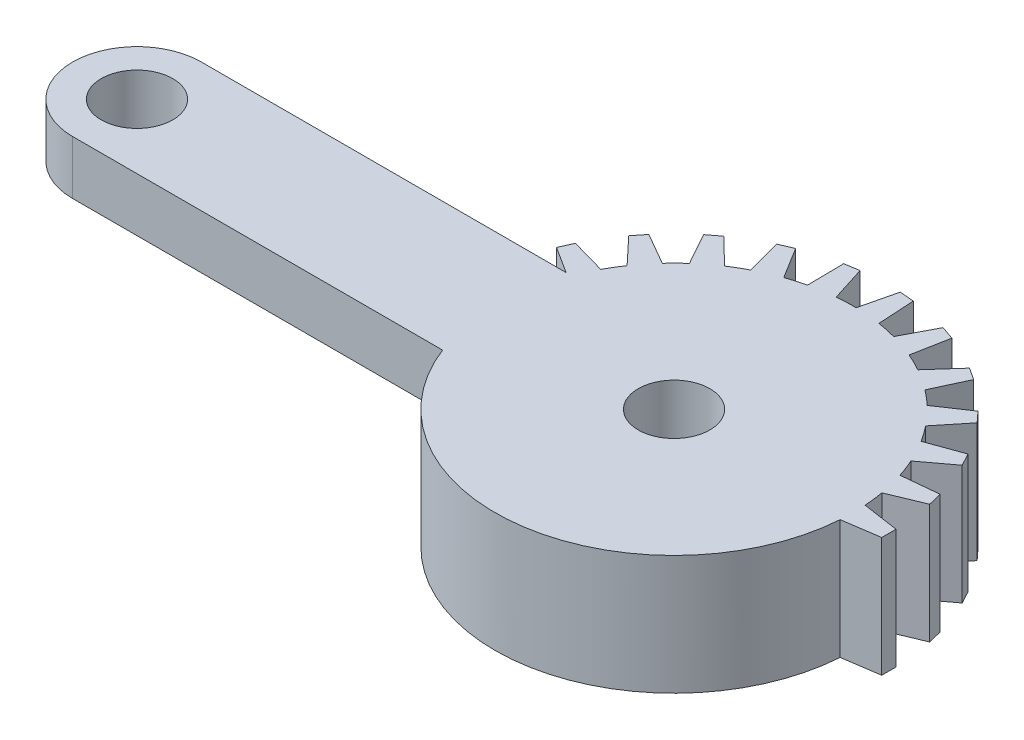
SolidWorks part; units mm, degrees
ref_plane "Front" through (0, 0, 0) normal (0, 0, 1) x (1, 0, 0)
ref_plane "Top" through (0, 0, 0) normal (0, 1, 0) x (1, 0, 0)
ref_plane "Right" through (0, 0, 0) normal (1, 0, 0) x (0, 0, -1)
sketch "Sketch1" plane through (0, 0, 0) normal (0, 1, 0) x (1, 0, 0)
  line L0 (-177.6425, 0) -> (70.7426, 0) construction
  line L1 (-150, 18) -> (-46.6476, 18)
  line L2 (-150, -18) -> (-46.6476, -18)
  arc A0 (-46.6476, -18) -> (-46.6476, 18) centre (0, 0) ccw
  arc A1 (-150, 18) -> (-150, -18) centre (-150, 0) ccw
  dimension "D1" = 100
  dimension "D3" = 150
  dimension "D2" = 18
extrude "Boss-Extrude1" add sketch "Sketch1" along normal blind 33.3333
sketch "Sketch2" plane through (0, 33.3333, 0) normal (0, 1, 0) x (1, 0, 0)
  line L0 (88.337, 0) -> (60, 0) construction
  line L1 (49.8773, 3.5) -> (60, 2)
  line L2 (60, 2) -> (60, -2)
  line L4 (50, 0) -> (49.8773, 3.5)
  line L5 (50, 0) -> (49.8773, -3.5)
  line L6 (49.8773, -3.5) -> (60, -2)
  line L7 (50, 0) -> (-74.3015, 0) construction
  line L8 (-46.6476, 18) -> (0, 0) construction
  arc A0 (-46.6476, -18) -> (-46.6476, 18) centre (0, 0) ccw construction
  arc A1 (49.8773, -3.5) -> (-46.6476, 18) centre (0, 0) ccw
  dimension "D1" = 4
  dimension "D2" = 10
  dimension "D3" = 3.5
extrude "Boss-Extrude2" add sketch "Sketch2" against normal up to surface (33.3333 mm away) contours L6 L2 L1 L4 L5 up to face at (-78.6619, 0, 0)
pattern_circular "CirPattern2" count 13 every 14.167 about axis through (0, 0, 0) along (0, 1, 0) of "Boss-Extrude2"
hole_wizard "Ø20.0mm 맞춤핀 구멍1" positions "Sketch4" profile "Sketch3" hole size "Ø20.0" standard "Ansi Metric" end condition through all
sketch "Sketch4" plane through (0, 33.3333, 0) normal (0, 1, 0) x (1, 0, 0)
  arc A0 (-150, 18) -> (-150, -18) centre (-150, 0) ccw construction
  point P0 (-150, 0)
  point P2 (0, 0)
  dimension "D1" = 0
sketch "Sketch3" plane through (-150, 33.3333, 0) normal (1, 0, 0) x (0, 0, 1)
  line L0 (0, 0) -> (0, 33.3333)
  line L1 (0, 33.3333) -> (10, 33.3333)
  line L2 (10, 33.3333) -> (10, 0)
  line L5 (10, 0) -> (0, 0)
  line L11 (0, -6.35) -> (0, 107.95) construction
  dimension "Thru Hole Dia." = 20
  dimension "Thru Hole Depth" = 33.3333
scale "축척1" scale about centroid uniform scaling yes scale factor 0.3
sketch "스케치1" plane through (0, 21.6667, 0) normal (0, 1, 0) x (1, 0, 0)
  line L0 (-36.6748, -4.0201) -> (-67.6805, -4.0201)
  line L2 (-37.1253, 6.7799) -> (-67.6805, 6.7799) construction
  line L3 (-67.6805, 6.7799) -> (-36.6748, 6.7799)
  arc A0 (-36.6748, 6.7799) -> (-36.6748, -4.0201) centre (-22.6805, 1.3799) ccw
  arc A1 (-67.6805, 6.7799) -> (-67.6805, -4.0201) centre (-67.6805, 1.3799) ccw construction
  arc A2 (-67.6805, 6.7799) -> (-67.6805, -4.0201) centre (-67.6805, 1.3799) ccw
extrude "컷-돌출1" cut sketch "스케치1" against normal blind 5.5 from offset 4.5
